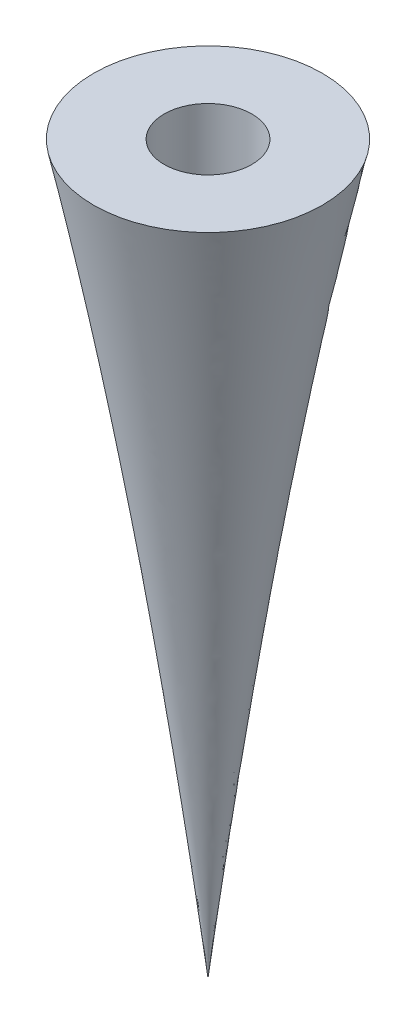
SolidWorks part; units mm, degrees
material "AISI 316 Annealed Stainless Steel Bar (SS)"
ref_plane "Front Plane" through (0, 0, 0) normal (0, 0, 1) x (1, 0, 0)
ref_plane "Top Plane" through (0, 0, 0) normal (0, 1, 0) x (1, 0, 0)
ref_plane "Right Plane" through (0, 0, 0) normal (1, 0, 0) x (0, 0, -1)
curve "Curve1"
  spline degree 3 poles (0, 0.6058, 14.8325) (0, 0.5941, 14.7866) (0, 0.5772, 14.7202) (0, 0.5557, 14.6369) (0, 0.5416, 14.5846) (0, 0.5291, 14.5387) (0, 0.5168, 14.4961) (0, 0.5048, 14.4554) (0, 0.4926, 14.4157) (0, 0.4802, 14.3766) (0, 0.4673, 14.3378) (0, 0.4538, 14.2991) (0, 0.44, 14.2601) (0, 0.4251, 14.2208) (0, 0.4098, 14.181) (0, 0.3934, 14.1406) (0, 0.3763, 14.0995) (0, 0.3581, 14.0576) (0, 0.3386, 14.015) (0, 0.3182, 13.9713) (0, 0.2963, 13.9267) (0, 0.2734, 13.8809) (0, 0.2489, 13.834) (0, 0.2226, 13.786) (0, 0.1951, 13.7365) (0, 0.1656, 13.6859) (0, 0.1343, 13.6338) (0, 0.1012, 13.5802) (0, 0.0658, 13.5252) (0, 0.0284, 13.4685) (0, -0.0115, 13.4102) (0, -0.0538, 13.3502) (0, -0.0989, 13.2885) (0, -0.1466, 13.2248) (0, -0.1973, 13.1592) (0, -0.2513, 13.0919) (0, -0.3084, 13.0222) (0, -0.3693, 12.9507) (0, -0.4336, 12.8768) (0, -0.5022, 12.8009) (0, -0.5747, 12.7226) (0, -0.6517, 12.6418) (0, -0.7333, 12.5586) (0, -0.8201, 12.473) (0, -0.9119, 12.3846) (0, -1.0094, 12.2937) (0, -1.1128, 12.1999) (0, -1.2223, 12.1032) (0, -1.3386, 12.0037) (0, -1.4617, 11.901) (0, -1.5923, 11.7953) (0, -1.7307, 11.6864) (0, -1.8774, 11.5742) (0, -2.0329, 11.4585) (0, -2.1978, 11.3394) (0, -2.3726, 11.2169) (0, -2.5577, 11.0905) (0, -2.7541, 10.9603) (0, -2.9623, 10.8264) (0, -3.1829, 10.6883) (0, -3.4169, 10.5464) (0, -3.6649, 10.4) (0, -3.9279, 10.2494) (0, -4.207, 10.0945) (0, -4.5028, 9.9348) (0, -4.8167, 9.7706) (0, -5.1498, 9.6017) (0, -5.5033, 9.4277) (0, -5.8785, 9.2488) (0, -6.2768, 9.0646) (0, -6.6999, 8.8753) (0, -7.1493, 8.6805) (0, -7.6269, 8.4801) (0, -8.1346, 8.2742) (0, -8.6743, 8.0622) (0, -9.2486, 7.8445) (0, -9.8597, 7.6204) (0, -10.5102, 7.3901) (0, -11.2033, 7.1535) (0, -11.9418, 6.9102) (0, -12.7294, 6.6604) (0, -13.5696, 6.4035) (0, -14.4667, 6.1396) (0, -15.425, 5.8686) (0, -16.4496, 5.59) (0, -17.5459, 5.3041) (0, -18.7197, 5.0102) (0, -19.9779, 4.7087) (0, -21.3276, 4.399) (0, -22.7771, 4.0809) (0, -24.3355, 3.7545) (0, -26.0129, 3.4195) (0, -27.8206, 3.0755) (0, -29.7714, 2.7227) (0, -31.8798, 2.3605) (0, -34.1622, 1.989) (0, -36.637, 1.6077) (0, -39.3255, 1.2168) (0, -42.252, 0.8158) (0, -45.4444, 0.4033) (0, -47.6661, 0.1383) (0, -48.8258, 0) knots 0 0 0 0 0.002686 0.003888 0.004874 0.005758 0.006588 0.007386 0.008167 0.00894 0.009711 0.010485 0.011266 0.012058 0.012864 0.013686 0.014528 0.01539 0.016276 0.017186 0.018124 0.019091 0.020092 0.021124 0.022194 0.0233 0.024449 0.025638 0.026873 0.028158 0.029491 0.030878 0.032322 0.033824 0.03539 0.037021 0.038721 0.040494 0.042345 0.044277 0.046294 0.048401 0.050602 0.052903 0.055311 0.057829 0.060465 0.063224 0.066114 0.069143 0.072314 0.07564 0.07913 0.082788 0.086628 0.09066 0.094894 0.099341 0.104016 0.10893 0.114098 0.119535 0.125259 0.131285 0.137632 0.144322 0.151373 0.15881 0.166659 0.174943 0.183694 0.19294 0.202718 0.213061 0.224006 0.2356 0.247885 0.26091 0.274732 0.289409 0.305002 0.321583 0.339229 0.358022 0.378056 0.399433 0.422263 0.446671 0.472795 0.500787 0.530818 0.563076 0.597777 0.635159 0.675491 0.719082 0.766278 0.817477 0.873132 0.933772 1 1 1 1
sketch "Sketch2" plane through (0, 0, 0) normal (1, 0, 0) x (0, 0, -1)
  line L0 (-10, 20) -> (-10, 79.984)
  line L1 (-10, 79.984) -> (-1.5875, 79.984)
  line L2 (-1.5875, 79.984) -> (-1.5875, -22.5)
  line L3 (-1.5875, -22.5) -> (-4.143, -22.5)
  line L4 (0, -48.8258) -> (0, 83.4498)
  line L5 (-1.5875, -22.5) -> (-1.5875, -27.1568)
  line L6 (-1.5875, -27.1568) -> (0, -27.1568)
  arc A0 (-15.925, 4.0841) -> (-14.8325, 0.6058) centre (-14.3036, 2.6827) ccw
  arc A2 (-15.925, 4.0841) -> (-10, 20) centre (-34.3392, 20) ccw
  spline S0 degree 3 poles (442.7753, 1947.2807) (-39.7264, -1.3009) (-26.1953, 3.5473) (-14.6369, 0.5557) (-14.5846, 0.5416) (-14.5387, 0.5291) (-14.4961, 0.5168) (-14.4554, 0.5048) (-14.4157, 0.4926) (-14.3766, 0.4802) (-14.3378, 0.4673) (-14.2991, 0.4538) (-14.2601, 0.44) (-14.2208, 0.4251) (-14.181, 0.4098) (-14.1406, 0.3934) (-14.0995, 0.3763) (-14.0576, 0.3581) (-14.015, 0.3386) (-13.9713, 0.3182) (-13.9267, 0.2963) (-13.8809, 0.2734) (-13.834, 0.2489) (-13.786, 0.2226) (-13.7365, 0.1951) (-13.6859, 0.1656) (-13.6338, 0.1343) (-13.5802, 0.1012) (-13.5252, 0.0658) (-13.4685, 0.0284) (-13.4102, -0.0115) (-13.3502, -0.0538) (-13.2885, -0.0989) (-13.2248, -0.1466) (-13.1592, -0.1973) (-13.0919, -0.2513) (-13.0222, -0.3084) (-12.9507, -0.3693) (-12.8768, -0.4336) (-12.8009, -0.5022) (-12.7226, -0.5747) (-12.6418, -0.6517) (-12.5586, -0.7333) (-12.473, -0.8201) (-12.3846, -0.9119) (-12.2937, -1.0094) (-12.1999, -1.1128) (-12.1032, -1.2223) (-12.0037, -1.3386) (-11.901, -1.4617) (-11.7953, -1.5923) (-11.6864, -1.7307) (-11.5742, -1.8774) (-11.4585, -2.0329) (-11.3394, -2.1978) (-11.2169, -2.3726) (-11.0905, -2.5577) (-10.9603, -2.7541) (-10.8264, -2.9623) (-10.6883, -3.1829) (-10.5464, -3.4169) (-10.4, -3.6649) (-10.2494, -3.9279) (-10.0945, -4.207) (-9.9348, -4.5028) (-9.7706, -4.8167) (-9.6017, -5.1498) (-9.4277, -5.5033) (-9.2488, -5.8785) (-9.0646, -6.2768) (-8.8753, -6.6999) (-8.6805, -7.1493) (-8.4801, -7.6269) (-8.2742, -8.1346) (-8.0622, -8.6743) (-7.8445, -9.2486) (-7.6204, -9.8597) (-7.3901, -10.5102) (-7.1535, -11.2033) (-6.9102, -11.9418) (-6.6604, -12.7294) (-6.4035, -13.5696) (-6.1396, -14.4667) (-5.8686, -15.425) (-5.59, -16.4496) (-5.3041, -17.5459) (-5.0102, -18.7197) (-4.7087, -19.9779) (-4.399, -21.3276) (-4.0809, -22.7771) (-3.7545, -24.3355) (-3.4195, -26.0129) (-3.0755, -27.8206) (-2.7227, -29.7714) (-2.3605, -31.8798) (-1.989, -34.1622) (-1.6077, -36.637) (-1.2168, -39.3255) (-0.8158, -42.252) (9.9601, -125.6496) (-9.3783, -211.767) (1994.8812, -47.5876) knots -0.672122 -0.672122 -0.672122 -0.672122 0.002686 0.003888 0.004874 0.005758 0.006588 0.007386 0.008167 0.00894 0.009711 0.010485 0.011266 0.012058 0.012864 0.013686 0.014528 0.01539 0.016276 0.017186 0.018124 0.019091 0.020092 0.021124 0.022194 0.0233 0.024449 0.025638 0.026873 0.028158 0.029491 0.030878 0.032322 0.033824 0.03539 0.037021 0.038721 0.040494 0.042345 0.044277 0.046294 0.048401 0.050602 0.052903 0.055311 0.057829 0.060465 0.063224 0.066114 0.069143 0.072314 0.07564 0.07913 0.082788 0.086628 0.09066 0.094894 0.099341 0.104016 0.10893 0.114098 0.119535 0.125259 0.131285 0.137632 0.144322 0.151373 0.15881 0.166659 0.174943 0.183694 0.19294 0.202718 0.213061 0.224006 0.2356 0.247885 0.26091 0.274732 0.289409 0.305002 0.321583 0.339229 0.358022 0.378056 0.399433 0.422263 0.446671 0.472795 0.500787 0.530818 0.563076 0.597777 0.635159 0.675491 0.719082 0.766278 0.817477 0.873132 0.933772 5.58568 5.58568 5.58568 5.58568 only from (-14.8325, 0.6058) to (0, -48.8258) construction
  spline S1 degree 3 poles (-14.8325, 0.6058) (-14.7866, 0.5941) (-14.7202, 0.5772) (-14.6369, 0.5557) (-14.5846, 0.5416) (-14.5387, 0.5291) (-14.4961, 0.5168) (-14.4554, 0.5048) (-14.4157, 0.4926) (-14.3766, 0.4802) (-14.3378, 0.4673) (-14.2991, 0.4538) (-14.2601, 0.44) (-14.2208, 0.4251) (-14.181, 0.4098) (-14.1406, 0.3934) (-14.0995, 0.3763) (-14.0576, 0.3581) (-14.015, 0.3386) (-13.9713, 0.3182) (-13.9267, 0.2963) (-13.8809, 0.2734) (-13.834, 0.2489) (-13.786, 0.2226) (-13.7365, 0.1951) (-13.6859, 0.1656) (-13.6338, 0.1343) (-13.5802, 0.1012) (-13.5252, 0.0658) (-13.4685, 0.0284) (-13.4102, -0.0115) (-13.3502, -0.0538) (-13.2885, -0.0989) (-13.2248, -0.1466) (-13.1592, -0.1973) (-13.0919, -0.2513) (-13.0222, -0.3084) (-12.9507, -0.3693) (-12.8768, -0.4336) (-12.8009, -0.5022) (-12.7226, -0.5747) (-12.6418, -0.6517) (-12.5586, -0.7333) (-12.473, -0.8201) (-12.3846, -0.9119) (-12.2937, -1.0094) (-12.1999, -1.1128) (-12.1032, -1.2223) (-12.0037, -1.3386) (-11.901, -1.4617) (-11.7953, -1.5923) (-11.6864, -1.7307) (-11.5742, -1.8774) (-11.4585, -2.0329) (-11.3394, -2.1978) (-11.2169, -2.3726) (-11.0905, -2.5577) (-10.9603, -2.7541) (-10.8264, -2.9623) (-10.6883, -3.1829) (-10.5464, -3.4169) (-10.4, -3.6649) (-10.2494, -3.9279) (-10.0945, -4.207) (-9.9348, -4.5028) (-9.7706, -4.8167) (-9.6017, -5.1498) (-9.4277, -5.5033) (-9.2488, -5.8785) (-9.0646, -6.2768) (-8.8753, -6.6999) (-8.6805, -7.1493) (-8.4801, -7.6269) (-8.2742, -8.1346) (-8.0622, -8.6743) (-7.8445, -9.2486) (-7.6204, -9.8597) (-7.3901, -10.5102) (-7.1535, -11.2033) (-6.9102, -11.9418) (-6.6604, -12.7294) (-6.4035, -13.5696) (-6.1396, -14.4667) (-5.8686, -15.425) (-5.59, -16.4496) (-5.3041, -17.5459) (-5.0102, -18.7197) (-4.7087, -19.9779) (-4.399, -21.3276) (-4.0809, -22.7771) (-3.7545, -24.3355) (-3.4195, -26.0129) (-3.0755, -27.8206) (-2.7227, -29.7714) (-2.3605, -31.8798) (-1.989, -34.1622) (-1.6077, -36.637) (-1.2168, -39.3255) (-0.8158, -42.252) (-0.4033, -45.4444) (-0.1383, -47.6661) (0, -48.8258) knots 0 0 0 0 0.002686 0.003888 0.004874 0.005758 0.006588 0.007386 0.008167 0.00894 0.009711 0.010485 0.011266 0.012058 0.012864 0.013686 0.014528 0.01539 0.016276 0.017186 0.018124 0.019091 0.020092 0.021124 0.022194 0.0233 0.024449 0.025638 0.026873 0.028158 0.029491 0.030878 0.032322 0.033824 0.03539 0.037021 0.038721 0.040494 0.042345 0.044277 0.046294 0.048401 0.050602 0.052903 0.055311 0.057829 0.060465 0.063224 0.066114 0.069143 0.072314 0.07564 0.07913 0.082788 0.086628 0.09066 0.094894 0.099341 0.104016 0.10893 0.114098 0.119535 0.125259 0.131285 0.137632 0.144322 0.151373 0.15881 0.166659 0.174943 0.183694 0.19294 0.202718 0.213061 0.224006 0.2356 0.247885 0.26091 0.274732 0.289409 0.305002 0.321583 0.339229 0.358022 0.378056 0.399433 0.422263 0.446671 0.472795 0.500787 0.530818 0.563076 0.597777 0.635159 0.675491 0.719082 0.766278 0.817477 0.873132 0.933772 1 1 1 1
  dimension "D3" = 59.984
  dimension "D1" = 20
  dimension "D2" = 10
  dimension "D4" = 22.5
  dimension "D5" = 1.5875
revolve "Revolve1" add sketch "Sketch2" angle 360 about L4
equation "\"r_cc_inner\"= 10'combustion chamber inner radius [mm]"
equation "\"r_cc_outer\"= 24'combustion chamber outer radius [mm]"
equation "\"L_star\"= 1500'combustion process characteristic length [mm]"
equation "\"At\"= 0.0000598 * ( 1000 ) ^ 2'Throat Area [mm^2]"
equation "\"x_cc\"= \"L_star\" * \"At\" / ( pi * ( \"r_cc_outer\" ^ 2 - \"r_cc_inner\" ^ 2 ) )'combustion chamber physical length [mm]"
equation "\"x_convergent\"= 20'length of the convergent section of the nozzle [mm]"
equation "\"r_throat\"= 15'outer radius of throat gap [mm]"
equation "\"x_material_change\"= 1.5 * \"r_throat\"'distance below throat at which nozzle material changes to a low-temp material [mm]"
equation "\"t_i\"= 8'insulation thickness required by thermal considerations [mm]"
equation "\"t_cw\"= 4'pressure vessle cylinder wall thickness required by structural considerations [mm]"
equation "\"t_p\" = 1 / 4 * 25.4'pressure vessle plate thickness required by structural considerations [mm]"
equation "\"r_outer\"= \"r_cc_outer\" + \"t_i\" + \"t_cw\" + 10'overall outermost radius of engine [mm]"
equation "\"D1@Sketch2\"=\"x_convergent\""
equation "\"D2@Sketch2\"=\"r_cc_inner\""
equation "\"D3@Sketch2\"=\"x_cc\""
equation "\"r_rod\"= 1 / 8 * 25.4 / 2'radius of the threaded rod in the center fo the spike [mm]"
equation "\"D4@Sketch2\"=\"x_material_change\""
equation "\"D5@Sketch2\"=\"r_rod\""
